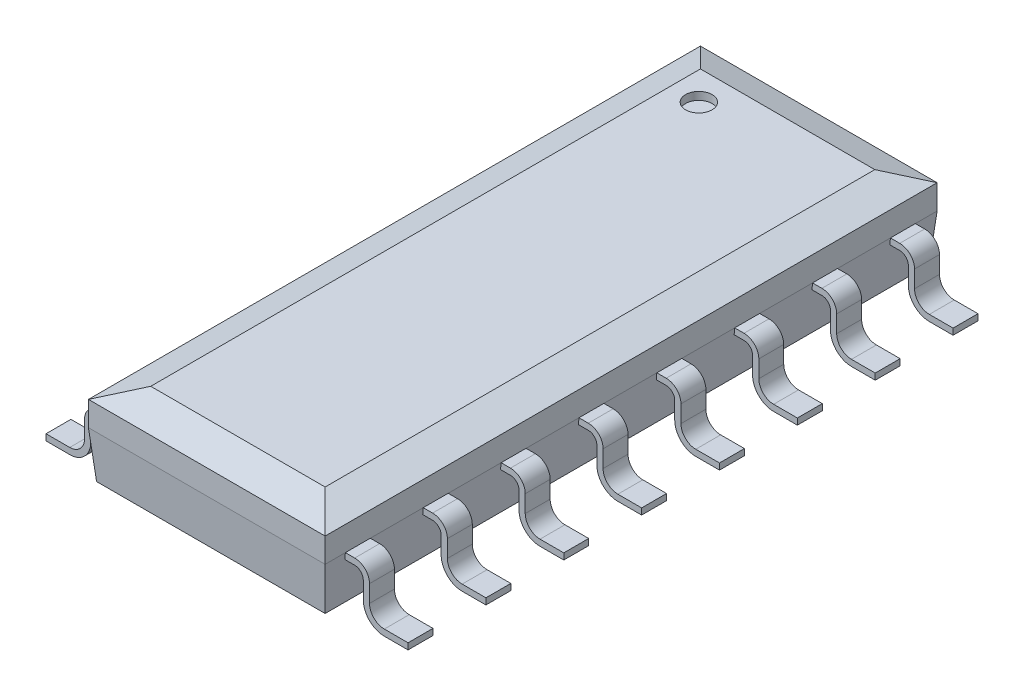
SolidWorks part; units mm, degrees
ref_plane "Front Plane" through (0, 0, 0) normal (0, 0, 1) x (1, 0, 0)
ref_plane "Top Plane" through (0, 0, 0) normal (0, 1, 0) x (1, 0, 0)
ref_plane "Right Plane" through (0, 0, 0) normal (1, 0, 0) x (0, 0, -1)
ref_plane "Plane 1" through (0.762, 0, 0) normal (1, 0, 0) x (0, 0, -1)
sketch "Sketch1" plane through (0.762, 0, 0) normal (1, 0, 0) x (0, 0, -1)
  line L1 (0.5588, 1.4478) -> (-9.4234, 1.4478)
  line L2 (0.5588, 1.4478) -> (0.5588, 0.1016)
  line L3 (0.5588, 0.1016) -> (-9.4234, 0.1016)
  line L4 (-9.4234, 1.4478) -> (-9.4234, 0.1016)
  dimension "D1" = 9.9822
  dimension "D2" = 1.3462
  dimension "D3" = 0.1016
  dimension "D4" = 0.5588
extrude "Base-Extrude" add sketch "Sketch1" along normal blind 3.8608
chamfer "Chamfer1" distance 0.508 angle 20 4 edges at (0.762, 1.4478, 4.4323) (4.6228, 1.4478, 4.4323) (2.6924, 1.4478, 9.4234) (2.6924, 1.4478, -0.5588)
chamfer "Chamfer2" distance 0.762 angle 5 4 edges at (4.6228, 0.1016, 4.4323) (0.762, 0.1016, 4.4323) (2.6924, 0.1016, -0.5588) (2.6924, 0.1016, 9.4234)
sketch "Sketch2" plane through (0, 1.4478, 0) normal (0, 1, 0) x (-1, 0, 0)
  line L0 (-4.1148, -0.0508) -> (-1.27, -0.0508) construction
  line L1 (-1.27, -0.0508) -> (-1.27, 8.9154) construction
  circle A0 centre (-1.7272, 0.4318) radius 0.2159
  dimension "D1" = 0.4318
  dimension "D3" = 0.4572
  dimension "D2" = 0.4826
extrude "Cut-Extrude1" cut sketch "Sketch2" against normal blind 0.127
ref_plane "Plane 2" through (2.6924, 0, 0) normal (-1, 0, 0) x (0, 0, 1)
sketch "Sketch3" plane through (0, 0, 0) normal (0, 0, 1) x (1, 0, 0)
  line L0 (1.4521, 0.8636) -> (0.6096, 0.8636)
  line L1 (0.6096, 0.8636) -> (0.6096, 1.9644) construction
  line L2 (1.3501, 0.6223) -> (-2.4338, 0.6223) construction
  line L3 (0.127, 0.1016) -> (-0.2603, 0.1016)
  line L4 (4.6228, 0.8636) -> (0.762, 0.8636) construction
  line L5 (0.3683, 0.6223) -> (0.3683, 0.3429)
  arc A0 (0.6096, 0.8636) -> (0.3683, 0.6223) centre (0.6096, 0.6223) ccw
  arc A1 (0.3683, 0.3429) -> (0.127, 0.1016) centre (0.127, 0.3429) cw
  dimension "D2" = 0.2413
  dimension "D1" = 0.1016
  dimension "D3" = 0.127
  dimension "D4" = 0.2794
extrude "Boss-Extrude-Thin1" add sketch "Sketch3" along normal mid plane 0.4064 thin thin type one direction reverse wall 0.1016
pattern_linear "LPattern1" count 8 spacing 1.27 along (0, 0, 1) of "Boss-Extrude-Thin1"
mirror "Mirror1" about plane through (2.6924, 0, 0) normal (-1, 0, 0) of "LPattern1", "Boss-Extrude-Thin1"
sketch "Component_Outline" plane through (0, 0, 0) normal (0, 1, 0) x (1, 0, 0)
  line L1 (-0.2603, -0.2032) -> (0.762, -0.2032)
  line L2 (2.6924, 0.5588) -> (2.6924, -9.4234) construction
  line L3 (-0.2603, -1.0668) -> (0.762, -1.0668)
  line L4 (0.762, -0.2032) -> (0.762, -1.0668)
  line L5 (-0.2603, -1.4732) -> (0.762, -1.4732)
  line L6 (-0.2603, -0.2032) -> (-0.2603, 0.2032)
  line L7 (-0.2603, -2.3368) -> (0.762, -2.3368)
  line L8 (0.762, -1.4732) -> (0.762, -2.3368)
  line L9 (-0.2603, -2.7432) -> (0.762, -2.7432)
  line L10 (-0.2603, -1.4732) -> (-0.2603, -1.0668)
  line L11 (-0.2603, -3.6068) -> (0.762, -3.6068)
  line L12 (0.762, -2.7432) -> (0.762, -3.6068)
  line L13 (-0.2603, -4.0132) -> (0.762, -4.0132)
  line L14 (-0.2603, -2.7432) -> (-0.2603, -2.3368)
  line L15 (-0.2603, -4.8768) -> (0.762, -4.8768)
  line L16 (0.762, -4.0132) -> (0.762, -4.8768)
  line L17 (-0.2603, -9.0932) -> (-0.2603, -8.6868)
  line L18 (-0.2603, -5.2832) -> (0.762, -5.2832)
  line L19 (-0.2603, -4.0132) -> (-0.2603, -3.6068)
  line L20 (-0.2603, -6.1468) -> (0.762, -6.1468)
  line L21 (0.762, -5.2832) -> (0.762, -6.1468)
  line L22 (-0.2603, -6.5532) -> (0.762, -6.5532)
  line L23 (-0.2603, -5.2832) -> (-0.2603, -4.8768)
  line L24 (-0.2603, -7.4168) -> (0.762, -7.4168)
  line L25 (0.762, -6.5532) -> (0.762, -7.4168)
  line L26 (-0.2603, -7.8232) -> (0.762, -7.8232)
  line L27 (-0.2603, -6.5532) -> (-0.2603, -6.1468)
  line L28 (-0.2603, -8.6868) -> (0.762, -8.6868)
  line L29 (0.762, -7.8232) -> (0.762, -8.6868)
  line L30 (0.762, 0.5588) -> (0.762, 0.2032)
  line L31 (0.762, 0.2032) -> (-0.2603, 0.2032)
  line L32 (0.762, -9.4234) -> (0.762, -9.0932)
  line L33 (0.762, -9.0932) -> (-0.2603, -9.0932)
  line L34 (-0.2603, -7.8232) -> (-0.2603, -7.4168)
  line L35 (0.762, 0.5588) -> (4.6228, 0.5588) construction
  line L36 (4.6228, -9.4234) -> (0.762, -9.4234) construction
  line L37 (5.6451, -7.8232) -> (5.6451, -7.4168)
  line L38 (4.6228, -9.0932) -> (5.6451, -9.0932)
  line L39 (4.6228, -9.4234) -> (4.6228, -9.0932)
  line L40 (4.6228, 0.2032) -> (5.6451, 0.2032)
  line L41 (4.6228, 0.5588) -> (4.6228, 0.2032)
  line L42 (4.6228, -7.8232) -> (4.6228, -8.6868)
  line L43 (5.6451, -8.6868) -> (4.6228, -8.6868)
  line L44 (5.6451, -6.5532) -> (5.6451, -6.1468)
  line L45 (5.6451, -7.8232) -> (4.6228, -7.8232)
  line L46 (4.6228, -6.5532) -> (4.6228, -7.4168)
  line L47 (5.6451, -7.4168) -> (4.6228, -7.4168)
  line L48 (5.6451, -5.2832) -> (5.6451, -4.8768)
  line L49 (5.6451, -6.5532) -> (4.6228, -6.5532)
  line L50 (4.6228, -5.2832) -> (4.6228, -6.1468)
  line L51 (5.6451, -6.1468) -> (4.6228, -6.1468)
  line L52 (5.6451, -4.0132) -> (5.6451, -3.6068)
  line L53 (5.6451, -5.2832) -> (4.6228, -5.2832)
  line L54 (5.6451, -9.0932) -> (5.6451, -8.6868)
  line L55 (4.6228, -4.0132) -> (4.6228, -4.8768)
  line L56 (5.6451, -4.8768) -> (4.6228, -4.8768)
  line L57 (5.6451, -2.7432) -> (5.6451, -2.3368)
  line L58 (5.6451, -4.0132) -> (4.6228, -4.0132)
  line L59 (4.6228, -2.7432) -> (4.6228, -3.6068)
  line L60 (5.6451, -3.6068) -> (4.6228, -3.6068)
  line L61 (5.6451, -1.4732) -> (5.6451, -1.0668)
  line L62 (5.6451, -2.7432) -> (4.6228, -2.7432)
  line L63 (4.6228, -1.4732) -> (4.6228, -2.3368)
  line L64 (5.6451, -2.3368) -> (4.6228, -2.3368)
  line L65 (5.6451, -0.2032) -> (5.6451, 0.2032)
  line L66 (5.6451, -1.4732) -> (4.6228, -1.4732)
  line L67 (4.6228, -0.2032) -> (4.6228, -1.0668)
  line L68 (5.6451, -1.0668) -> (4.6228, -1.0668)
  line L69 (5.6451, -0.2032) -> (4.6228, -0.2032)
  line L70 (0.762, 0.5588) -> (4.6228, 0.5588)
  line L71 (0.762, -9.4234) -> (4.6228, -9.4234)
